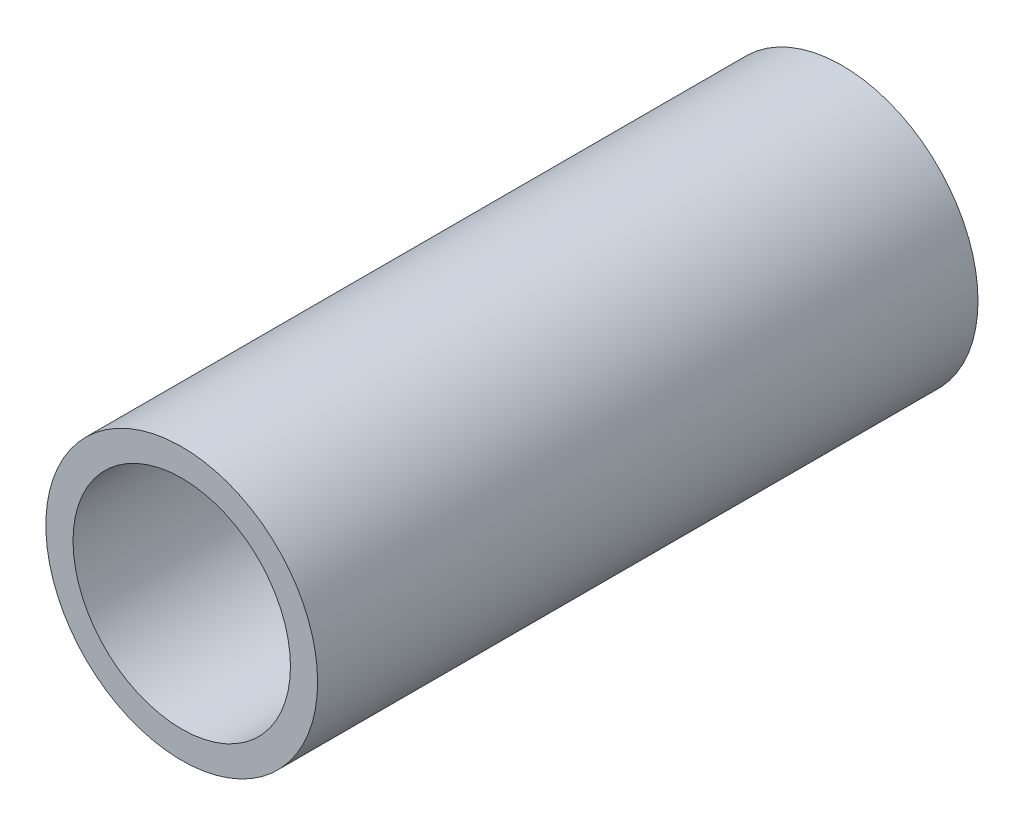
SolidWorks part; units mm, degrees
material "1.0037 (S235JR)"
ref_plane "Front Plane" through (0, 0, 0) normal (0, 0, 1) x (1, 0, 0)
ref_plane "Top Plane" through (0, 0, 0) normal (0, 1, 0) x (1, 0, 0)
ref_plane "Right Plane" through (0, 0, 0) normal (1, 0, 0) x (0, 0, -1)
sketch "Sketch1" plane through (0, 0, 0) normal (0, 0, 1) x (1, 0, 0)
  circle A0 centre (0, 0) radius 2.5
  circle A1 centre (0, 0) radius 2
  dimension "D1" = 4
  dimension "D2" = 5
extrude "Boss-Extrude1" add sketch "Sketch1" along normal blind 12.15
